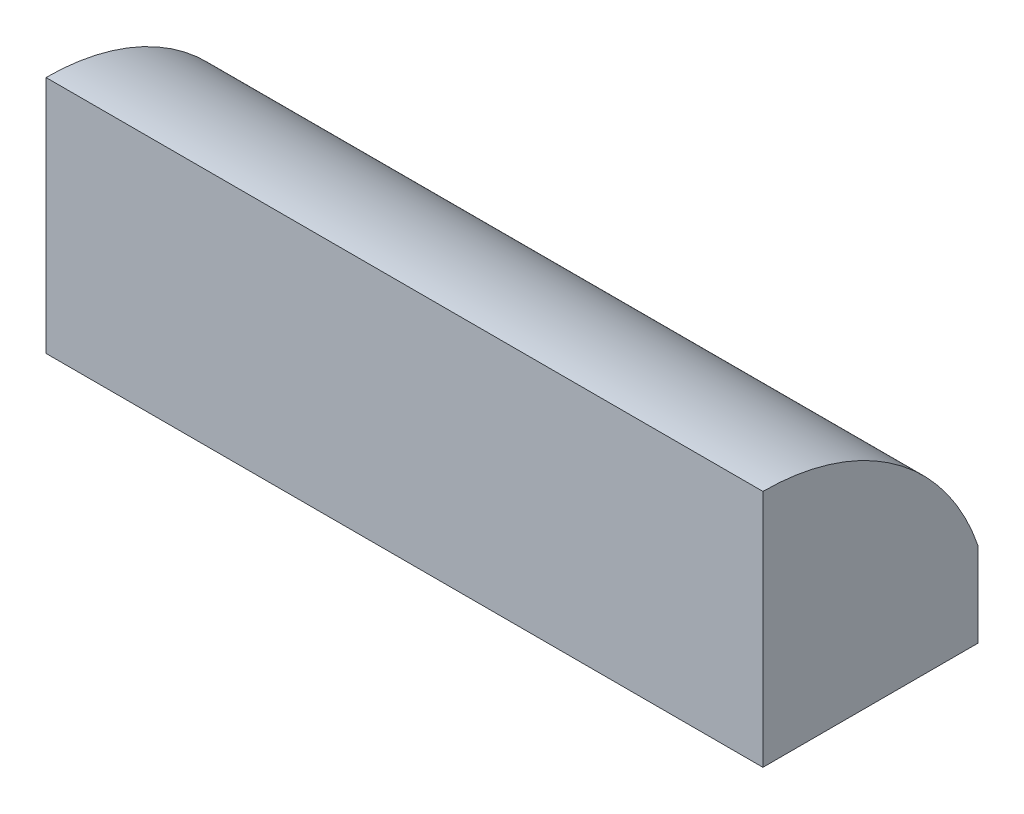
SolidWorks part; units mm, degrees
ref_plane "Front Plane" through (0, 0, 0) normal (0, 0, 1) x (1, 0, 0)
ref_plane "Top Plane" through (0, 0, 0) normal (0, 1, 0) x (1, 0, 0)
ref_plane "Right Plane" through (0, 0, 0) normal (1, 0, 0) x (0, 0, -1)
sketch "Sketch2" plane through (0, 0, 0) normal (0, 1, 0) x (1, 0, 0)
  line L1 (-10.7282, 10.277) -> (65.4718, 10.277)
  line L2 (-10.7282, 10.277) -> (-10.7282, -12.583)
  line L3 (-10.7282, -12.583) -> (65.4718, -12.583)
  line L4 (65.4718, 10.277) -> (65.4718, -12.583)
  dimension "D1" = 22.86
  dimension "D2" = 76.2
extrude "Boss-Extrude1" add sketch "Sketch2" along normal blind 25.4
sketch "Sketch3" plane through (65.4718, 0, 0) normal (1, 0, 0) x (0, 0, -1)
  line L3 (10.277, 25.4) -> (10.277, 0) construction
  line L4 (-12.583, 25.4) -> (10.277, 25.4)
  line L5 (10.277, 25.4) -> (10.277, 8.9634)
  arc A0 (-12.583, 25.4) -> (10.277, 8.9634) centre (-12.583, 1.2849) cw
extrude "Cut-Extrude1" cut sketch "Sketch3" against normal through all
